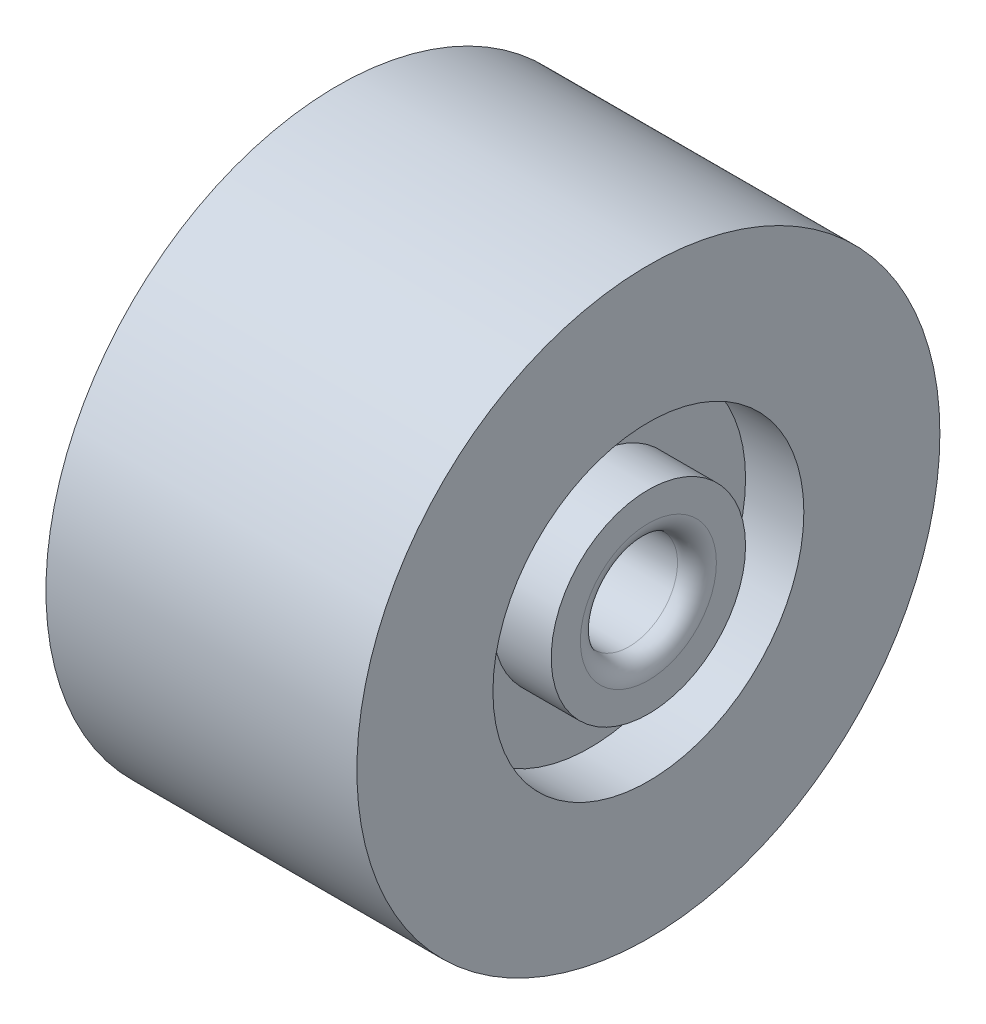
SolidWorks part; units mm, degrees
ref_plane "Front Plane" through (0, 0, 0) normal (0, 0, 1) x (1, 0, 0)
ref_plane "Top Plane" through (0, 0, 0) normal (0, 1, 0) x (1, 0, 0)
ref_plane "Right Plane" through (0, 0, 0) normal (1, 0, 0) x (0, 0, -1)
sketch "Sketch1" plane through (0, 0, 0) normal (0, 0, 1) x (1, 0, 0)
  line L0 (8.1873, -2.5) -> (-21.746, -2.5) construction
  line L1 (0, 2.5) -> (-3, 2.5)
  line L2 (-3, 2.5) -> (-3, 5.5)
  line L3 (-3, 5.5) -> (0, 5.5)
  line L4 (0, 5.5) -> (0, 12.5)
  line L5 (0, 12.5) -> (-16, 12.5)
  line L6 (-16, 12.5) -> (-16, 5.5)
  line L7 (-16, 5.5) -> (-13, 5.5)
  line L8 (-13, 5.5) -> (-13, 2.5)
  line L9 (-13, 2.5) -> (-16, 2.5)
  line L10 (-16, 2.5) -> (-16, -2.5)
  line L14 (-16, -2.5) -> (0, -2.5)
  line L15 (0, -2.5) -> (0, 2.5)
  dimension "D1" = 16
  dimension "D2" = 7
  dimension "D3" = 3
  dimension "D4" = 3
  dimension "D5" = 5
revolve "Revolve2" add sketch "Sketch1" angle 360 about L0
sketch "Sketch2" plane through (-16, 0, 0) normal (-1, 0, 0) x (0, 0, 1)
  circle A0 centre (0, -2.5) radius 2.5
extrude "Cut-Extrude1" cut sketch "Sketch2" against normal up to surface (16 mm away) up to face at (0, -2.5, -5)
fillet "Fillet1" radius 1 2 edges at (-16, -2.5, 2.5) (0, -2.5, -2.5)
